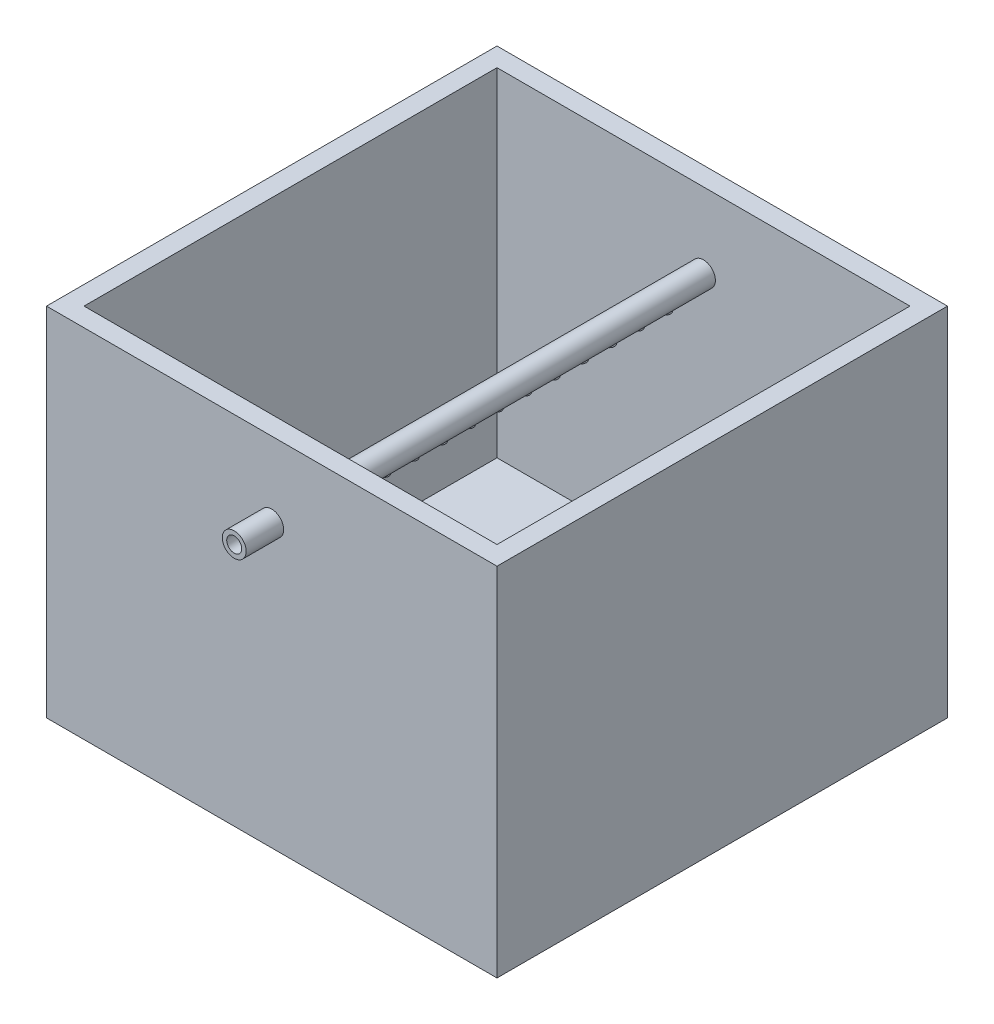
SolidWorks part; units mm, degrees
ref_plane "Front Plane" through (0, 0, 0) normal (0, 0, 1) x (1, 0, 0)
ref_plane "Top Plane" through (0, 0, 0) normal (0, 1, 0) x (1, 0, 0)
ref_plane "Right Plane" through (0, 0, 0) normal (1, 0, 0) x (0, 0, -1)
sketch "Sketch1" plane through (0, 0, 0) normal (0, 1, 0) x (1, 0, 0)
  line L1 (-60, -60) -> (60, -60)
  line L2 (-60, -60) -> (-60, 60)
  line L3 (-60, 60) -> (60, 60)
  line L4 (60, -60) -> (60, 60)
  line L5 (-60, -60) -> (60, 60) construction
  line L6 (-60, 60) -> (60, -60) construction
  point P0 (0, 0)
  dimension "D1" = 120
  dimension "D2" = 120
extrude "Boss-Extrude1" add sketch "Sketch1" along normal blind 150
shell "Shell1" thickness 5
sketch "Sketch2" plane through (0, 0, 60) normal (0, 0, 1) x (1, 0, 0)
  circle A0 centre (0, 75) radius 3.175
  circle A1 centre (0, 75) radius 2
  dimension "D1" = 6.35
  dimension "D2" = 4
extrude "Boss-Extrude2" add sketch "Sketch2" along normal blind 10 and the other way blind 116
sketch "Sketch3" plane through (0, 5, 0) normal (0, 1, 0) x (1, 0, 0)
  circle A0 centre (0, 0) radius 1
  circle A1 centre (0, 7.5) radius 1
  circle A2 centre (0, -7.5) radius 1
  circle A3 centre (0, -15) radius 1
  circle A4 centre (0, 15) radius 1
  circle A5 centre (0, -22.5) radius 1
  circle A6 centre (0, 22.5) radius 1
  circle A7 centre (0, -30) radius 1
  circle A8 centre (0, 30) radius 1
  circle A9 centre (0, -37.5) radius 1
  circle A10 centre (0, 37.5) radius 1
  circle A11 centre (0, -45) radius 1
  circle A12 centre (0, 45) radius 1
  dimension "D1" = 2
  dimension "D2" = 2
  dimension "D3" = 2
  dimension "D4" = 2
  dimension "D5" = 2
  dimension "D6" = 2
  dimension "D7" = 2
  dimension "D8" = 2
  dimension "D9" = 2
  dimension "D10" = 2
  dimension "D11" = 2
  dimension "D23" = 2
  dimension "D24" = 2
  dimension "D12" = 37.5
  dimension "D13" = 30
  dimension "D14" = 22.5
  dimension "D15" = 15
  dimension "D16" = 7.5
  dimension "D17" = 7.5
  dimension "D18" = 15
  dimension "D19" = 22.5
  dimension "D20" = 30
  dimension "D21" = 37.5
  dimension "D22" = 45
  dimension "D25" = 45
extrude "Cut-Extrude1" cut sketch "Sketch3" along normal blind 70
sketch "Sketch4" plane through (0, 0, 60) normal (0, 0, 1) x (1, 0, 0)
  line L0 (60, 150) -> (60, 0) construction
  line L1 (-60, 162.2431) -> (60, 162.2431)
  line L2 (-60, 162.2431) -> (-60, 95)
  line L3 (-60, 95) -> (60, 95)
  line L4 (60, 162.2431) -> (60, 95)
  line L5 (-60, 162.2431) -> (60, 95) construction
  line L6 (-60, 95) -> (60, 162.2431) construction
  circle A0 centre (0, 75) radius 2 construction
  point P0 (0, 128.6215)
  dimension "D1" = 20
extrude "Cut-Extrude2" cut sketch "Sketch4" against normal blind 120
sketch "Sketch5" plane through (-60, 0, 0) normal (-1, 0, 0) x (0, 0, 1)
  circle A0 centre (0, 27.5) radius 2
  circle A1 centre (0, 27.5) radius 3.175
  dimension "D1" = 4
  dimension "D2" = 6.35
extrude "Boss-Extrude3" add sketch "Sketch5" along normal blind 10
sketch "Sketch6" plane through (-60, 0, 0) normal (-1, 0, 0) x (0, 0, 1)
  circle A0 centre (0, 27.5) radius 2
extrude "Cut-Extrude3" cut sketch "Sketch6" against normal blind 10
sketch "Sketch7" plane through (0, 0, 70) normal (0, 0, 1) x (1, 0, 0)
  circle A1 centre (0, 75) radius 2
extrude "Cut-Extrude4" cut sketch "Sketch7" against normal blind 29
ref_plane "Plane2" through (0, 71.825, 0) normal (0, -1, 0) x (-1, 0, 0)
sketch "Sketch10" plane through (0, 71.825, 0) normal (0, -1, 0) x (-1, 0, 0)
  line L0 (-12.5763, 0) -> (13.9668, 0) construction
  circle A0 centre (0, 0) radius 1
  circle A1 centre (0, 7.5) radius 1
  circle A2 centre (0, 15) radius 1
  circle A3 centre (0, 22.5) radius 1
  circle A4 centre (0, 30) radius 1
  circle A5 centre (0, 37.5) radius 1
  circle A6 centre (0, 45) radius 1
  circle A7 centre (0, -45) radius 1
  circle A8 centre (0, -37.5) radius 1
  circle A9 centre (0, -30) radius 1
  circle A10 centre (0, -22.5) radius 1
  circle A11 centre (0, -15) radius 1
  circle A12 centre (0, -7.5) radius 1
  circle A13 centre (0, 45) radius 1.275
  circle A14 centre (0, 37.5) radius 1.235
  circle A15 centre (0, 30) radius 1.3227
  circle A16 centre (0, 22.5) radius 1.2863
  circle A17 centre (0, 15) radius 1.295
  circle A18 centre (0, 7.5) radius 1.1963
  circle A19 centre (0, 0) radius 1.1532
  circle A20 centre (0, -7.5) radius 1.2272
  circle A21 centre (0, -15) radius 1.2541
  circle A22 centre (0, -22.5) radius 1.2359
  circle A23 centre (0, -30) radius 1.184
  circle A24 centre (0, -37.5) radius 1.1949
  circle A25 centre (0, -45) radius 1.2442
  dimension "D1" = 2
  dimension "D2" = 2
  dimension "D3" = 2
  dimension "D4" = 2
  dimension "D5" = 2
  dimension "D6" = 2
  dimension "D7" = 2
  dimension "D8" = 7.5
  dimension "D9" = 7.5
  dimension "D10" = 7.5
  dimension "D11" = 7.5
  dimension "D12" = 7.5
  dimension "D13" = 7.5
extrude "Boss-Extrude4" add sketch "Sketch10" along normal blind 0.5 and the other way blind 1
